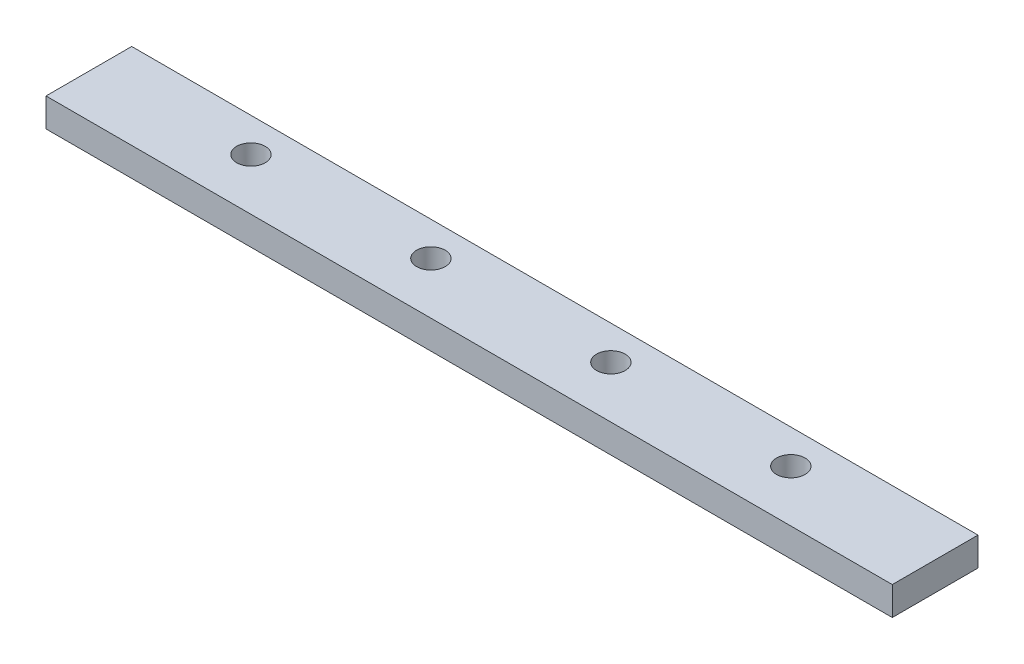
SolidWorks part; units mm, degrees
ref_plane "Front Plane" through (0, 0, 0) normal (0, 0, 1) x (1, 0, 0)
ref_plane "Top Plane" through (0, 0, 0) normal (0, 1, 0) x (1, 0, 0)
ref_plane "Right Plane" through (0, 0, 0) normal (1, 0, 0) x (0, 0, -1)
sketch "Sketch1" plane through (0, 0, 0) normal (1, 0, 0) x (0, 0, -1)
  line L1 (0, 0) -> (38.1, 0)
  line L2 (0, 0) -> (0, 12.7)
  line L3 (0, 12.7) -> (38.1, 12.7)
  line L4 (38.1, 0) -> (38.1, 12.7)
  dimension "D1" = 38.1
  dimension "D2" = 12.7
extrude "Boss-Extrude1" add sketch "Sketch1" along normal blind 376.2
sketch "Sketch2" plane through (0, 12.7, 0) normal (0, 1, 0) x (1, 0, 0)
  line L0 (376.2, 23) -> (308.1, 23) construction
  line L1 (376.2, 38.1) -> (376.2, 0) construction
  line L2 (308.1, 23) -> (228.1, 23) construction
  line L3 (228.1, 23) -> (148.1, 23) construction
  line L4 (148.1, 23) -> (68.1, 23) construction
  line L5 (68.1, 23) -> (0, 23) construction
  line L6 (0, 38.1) -> (0, 0) construction
  line L8 (376.2, 38.1) -> (0, 38.1) construction
  circle A0 centre (308.1, 23) radius 6.35
  circle A1 centre (228.1, 23) radius 6.35
  circle A2 centre (148.1, 23) radius 6.35
  circle A3 centre (68.1, 23) radius 6.35
  dimension "D2" = 12.7
  dimension "D1" = 15.1
  dimension "D3" = 68.1
extrude "Cut-Extrude1" cut sketch "Sketch2" against normal through all both and the other way through all
